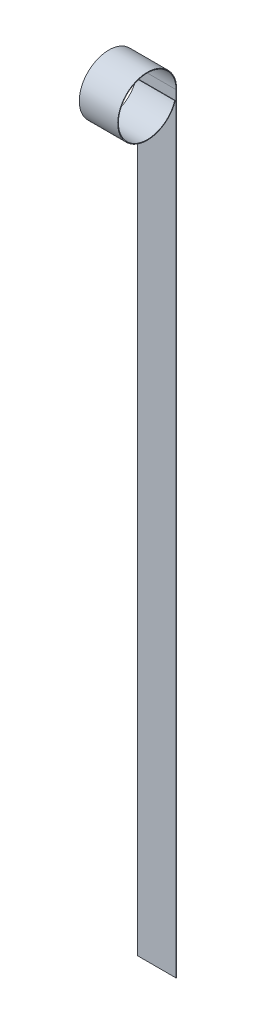
SolidWorks part; units mm, degrees
ref_plane "Front" through (0, 0, 0) normal (0, 0, 1) x (1, 0, 0)
ref_plane "Top" through (0, 0, 0) normal (0, 1, 0) x (1, 0, 0)
ref_plane "Right" through (0, 0, 0) normal (1, 0, 0) x (0, 0, -1)
sketch "Sketch1" plane through (0, 0, 0) normal (1, 0, 0) x (0, 0, -1)
  line L0 (28.575, 0) -> (28.575, -762)
  arc A1 (28.575, 0) -> (27.2149, -8.711) centre (0, 0) ccw
  dimension "D1" = 57.15
  dimension "D2" = 762
extrude "Extrude-Thin2" add sketch "Sketch1" along normal mid plane 38.1 thin thin type one direction wall 0.635
